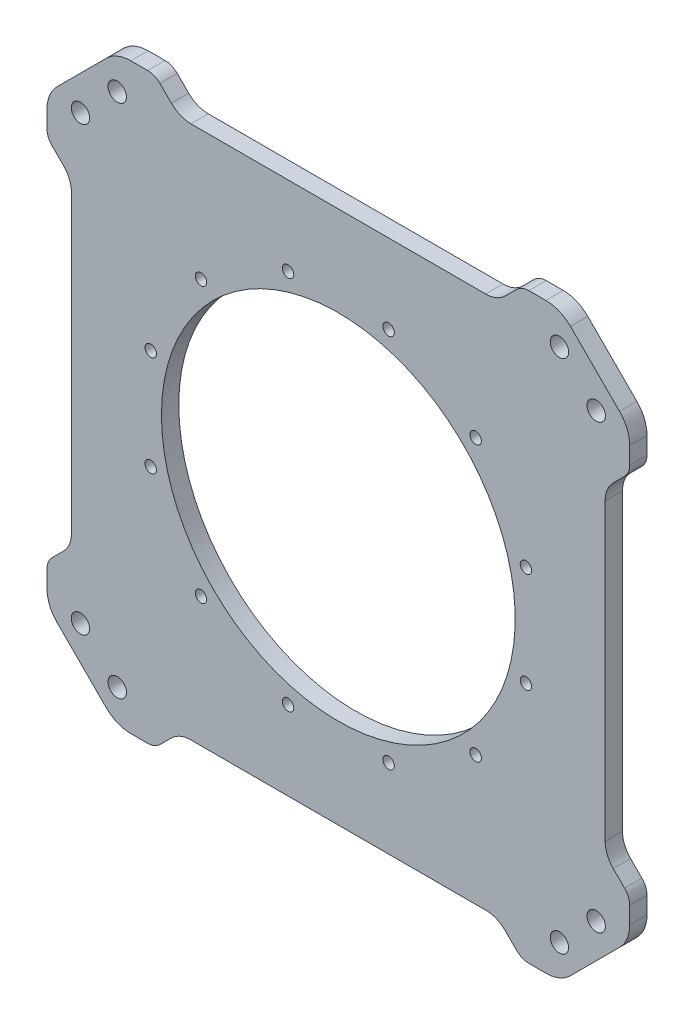
SolidWorks part; units mm, degrees
material "Hexcel AS4C (3000 丝)"
ref_plane "前视基准面" through (0, 0, 0) normal (0, 0, 1) x (1, 0, 0)
ref_plane "上视基准面" through (0, 0, 0) normal (0, 1, 0) x (1, 0, 0)
ref_plane "右视基准面" through (0, 0, 0) normal (1, 0, 0) x (0, 0, -1)
sketch "草图1" plane through (0, 0, 0) normal (0, 0, 1) x (1, 0, 0)
  line L0 (-84, 84) -> (-84, -84)
  line L1 (-64.3467, 64.3467) -> (64.3467, 64.3467) construction
  line L2 (-64.3467, 64.3467) -> (-64.3467, -64.3467) construction
  line L3 (-64.3467, -64.3467) -> (64.3467, -64.3467) construction
  line L4 (64.3467, 64.3467) -> (64.3467, -64.3467) construction
  line L5 (-64.3467, 64.3467) -> (64.3467, -64.3467) construction
  line L6 (-64.3467, -64.3467) -> (64.3467, 64.3467) construction
  line L7 (-84, -84) -> (84, -84)
  line L8 (84, 84) -> (84, -84)
  line L9 (-84, 84) -> (84, 84)
  circle A0 centre (0, 0) radius 91 construction
  dimension "D1" = 182
  dimension "D2" = 168
extrude "凸台-拉伸1" add sketch "草图1" along normal blind 5
sketch "草图2" plane through (0, 0, 5) normal (0, 0, 1) x (1, 0, 0)
  line L0 (64, 84) -> (84, 64)
  line L1 (84, 84) -> (-84, 84) construction
  line L2 (84, -84) -> (84, 84) construction
  line L3 (84, 64) -> (84, 84)
  line L4 (84, 84) -> (64, 84)
  line L5 (64, -84) -> (84, -84)
  line L6 (84, -84) -> (84, -64)
  line L7 (84, -64) -> (64, -84)
  line L8 (-84, -64) -> (-84, -84)
  line L9 (-84, -84) -> (-64, -84)
  line L10 (-64, -84) -> (-84, -64)
  line L11 (-64, 84) -> (-84, 84)
  line L12 (-84, 84) -> (-84, 64)
  line L13 (-84, 64) -> (-64, 84)
  circle A0 centre (0, 0) radius 91 construction
  point P23 (0, 0)
  dimension "D1" = 182
  dimension "D2" = 20
  dimension "D3" = 4
extrude "切除-拉伸1" cut sketch "草图2" against normal through all
sketch "草图3" plane through (0, 0, 5) normal (0, 0, 1) x (1, 0, 0)
  line L0 (0, 0) -> (0, 25) construction
  line L1 (0, 0) -> (10.2555, 38.2742) construction
  circle A0 centre (0, 0) radius 29 construction
  circle A1 centre (7.5058, 28.0118) radius 2.1
  circle A2 centre (0, 0) radius 25
  dimension "D1" = 58
  dimension "D2" = 4.2
  dimension "D3" = 50
  dimension "D4" = 15
extrude "切除-拉伸2" [suppressed] cut sketch "草图3" against normal through all
sketch "草图4" plane through (0, 0, 0) normal (0, 0, -1) x (-1, 0, 0)
  line L0 (-84, 0) -> (84, 0) construction
  line L1 (-84, -64) -> (-84, 64) construction
  line L2 (84, 64) -> (84, -64) construction
  line L3 (0, 84) -> (0, -84) construction
  line L4 (-64, 84) -> (64, 84) construction
  line L5 (64, -84) -> (-64, -84) construction
  circle A0 centre (64, 0) radius 2.15
  circle A1 centre (74, 0) radius 2.15
  circle A2 centre (54, 0) radius 2.15
  circle A3 centre (0, -54) radius 2.15
  circle A4 centre (0, -64) radius 2.15
  circle A5 centre (0, -74) radius 2.15
  circle A6 centre (-54, 0) radius 2.15
  circle A7 centre (-64, 0) radius 2.15
  circle A8 centre (-74, 0) radius 2.15
  circle A9 centre (0, 54) radius 2.15
  circle A10 centre (0, 64) radius 2.15
  circle A11 centre (0, 74) radius 2.15
  point P39 (0, 0)
  dimension "D1" = 4.3
  dimension "D2" = 10
  dimension "D3" = 10
  dimension "D4" = 10
  dimension "D5" = 4
extrude "切除-拉伸3" [suppressed] cut sketch "草图4" against normal through all
pattern_circular "阵列(圆周)1" [suppressed] count 12 over 360
sketch "草图5" plane through (0, 0, 0) normal (0, 0, -1) x (-1, 0, 0)
  circle A0 centre (0, 0) radius 51
  dimension "D1" = 102
extrude "切除-拉伸4" cut sketch "草图5" against normal through all
sketch "草图6" plane through (0, 0, 0) normal (0, 0, -1) x (-1, 0, 0)
  line L0 (-74, 74) -> (74, -74) construction
  line L1 (-64, 84) -> (-84, 64) construction
  line L2 (64, -84) -> (84, -64) construction
  line L3 (-74, -74) -> (74, 74) construction
  line L4 (-84, -64) -> (-64, -84) construction
  line L5 (84, 64) -> (64, 84) construction
  circle A0 centre (-39.598, -39.598) radius 1.65
  circle A1 centre (0, 0) radius 56 construction
  dimension "D1" = 112
  dimension "D2" = 3.3
extrude "切除-拉伸5" cut sketch "草图6" against normal through all
pattern_circular "阵列(圆周)2" count 12 over 360 about axis through (0, 0, 0) along (0, 0, 1) of "切除-拉伸5"
sketch "草图7" plane through (0, 0, 0) normal (0, 0, -1) x (-1, 0, 0)
  line L0 (54.1005, 84) -> (84, 54.1005) construction
  line L1 (-64, 84) -> (64, 84) construction
  line L2 (84, 64) -> (84, -64) construction
  line L3 (84, 64) -> (64, 84) construction
  line L4 (69.0503, 69.0503) -> (90.7732, 90.7732) construction
  circle A0 centre (74.3536, 63.747) radius 2.65
  circle A1 centre (63.747, 74.3536) radius 2.65
  circle A2 centre (69.0503, 69.0503) radius 2.65 construction
  dimension "D2" = 5.3
  dimension "D3" = 15
  dimension "D1" = 7
extrude "切除-拉伸6" cut sketch "草图7" against normal through all
pattern_circular "阵列(圆周)3" count 4 over 360 about axis through (0, 0, 0) along (0, 0, 1) of "切除-拉伸6"
fillet "圆角1" radius 10 8 edges at (84, 64, 2.5) (64, 84, 2.5) (-84, 64, 2.5) (-64, 84, 2.5) (-64, -84, 2.5) (-84, -64, 2.5) (84, -64, 2.5) (64, -84, 2.5)
sketch "草图8" plane through (0, 0, 0) normal (0, 0, -1) x (-1, 0, 0)
  line L0 (-84, -59.8579) -> (-84, 59.8579) construction
  line L1 (-59.8579, 84) -> (59.8579, 84) construction
  line L2 (-66.9289, 81.0711) -> (-81.0711, 66.9289) construction
  line L3 (-84, -52.8873) -> (-84, 52.8873)
  line L4 (-52.8873, 84) -> (52.8873, 84)
  line L5 (-66.9289, 81.0711) -> (-81.0711, 66.9289) construction
  line L6 (-74, 74) -> (-46.2304, 46.2304) construction
  line L7 (-84, 52.8873) -> (-76.9289, 45.8162)
  line L8 (-52.8873, 84) -> (-45.8162, 76.9289)
  line L9 (0, 0) -> (0, 132.697) construction
  line L10 (84, 52.8873) -> (76.9289, 45.8162)
  line L11 (52.8873, 84) -> (45.8162, 76.9289)
  line L12 (84, 59.8579) -> (84, -59.8579) construction
  line L14 (84, 52.8873) -> (84, -52.8873)
  line L16 (-45.8162, 76.9289) -> (45.8162, 76.9289)
  line L18 (59.8579, -84) -> (-59.8579, -84) construction
  line L21 (52.8873, -84) -> (-52.8873, -84)
  line L23 (0, 0) -> (142.172, 0) construction
  line L24 (84, -52.8873) -> (76.9289, -45.8162)
  line L25 (52.8873, -84) -> (45.8162, -76.9289)
  line L26 (-52.8873, -84) -> (-45.8162, -76.9289)
  line L27 (-84, -52.8873) -> (-76.9289, -45.8162)
  line L28 (76.9289, -45.8162) -> (76.9289, 45.8162)
  line L29 (45.8162, -76.9289) -> (-45.8162, -76.9289)
  line L30 (-76.9289, -45.8162) -> (-76.9289, 45.8162)
  dimension "D1" = 22
  dimension "D2" = 10
extrude "切除-拉伸7" cut sketch "草图8" against normal through all and the other way through all
fillet "圆角2" radius 8 8 edges at (45.8162, -76.9289, 2.5) (-45.8162, -76.9289, 2.5) (-76.9289, -45.8162, 2.5) (-76.9289, 45.8162, 2.5) (-45.8162, 76.9289, 2.5) (45.8162, 76.9289, 2.5) (76.9289, 45.8162, 2.5) (76.9289, -45.8162, 2.5)
fillet "圆角3" radius 5 8 edges at (84, -52.8873, 2.5) (52.8873, -84, 2.5) (-52.8873, -84, 2.5) (-84, -52.8873, 2.5) (-84, 52.8873, 2.5) (-52.8873, 84, 2.5) (52.8873, 84, 2.5) (84, 52.8873, 2.5)
